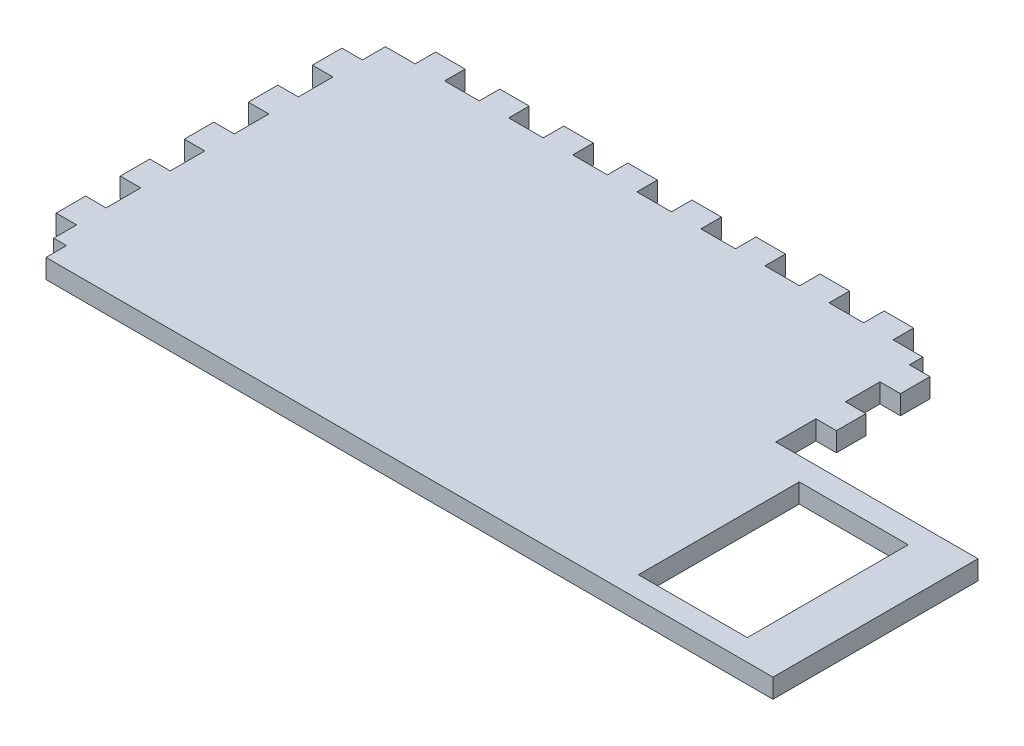
SolidWorks part; units mm, degrees
ref_plane "Front Plane" through (0, 0, 0) normal (0, 0, 1) x (1, 0, 0)
ref_plane "Top Plane" through (0, 0, 0) normal (0, 1, 0) x (1, 0, 0)
ref_plane "Right Plane" through (0, 0, 0) normal (1, 0, 0) x (0, 0, -1)
sketch "Sketch1" plane through (0, 0, 0) normal (0, 1, 0) x (1, 0, 0)
  line L63 (-28.8972, -2.2822) -> (-28.8972, -7.6797)
  line L64 (-28.8972, 35.9003) -> (-24.2472, 35.9003)
  line L65 (-28.8972, 35.9003) -> (-28.8972, 32.3103)
  line L66 (-28.8972, 7.7153) -> (-28.8972, 2.3178)
  line L67 (-28.8972, -15.8697) -> (-26.8972, -15.8697)
  line L68 (-28.8972, 17.7128) -> (-28.8972, 12.3153)
  line L69 (55.0028, 35.9003) -> (55.0028, 33.8003)
  line L70 (-28.8972, 27.7103) -> (-28.8972, 22.3128)
  line L71 (-28.8972, -7.6797) -> (-32.0972, -7.6797)
  line L73 (-28.8972, -12.2797) -> (-32.0972, -12.2797)
  line L74 (-32.0972, -7.6797) -> (-32.0972, -12.2797)
  line L75 (-28.8972, 2.3178) -> (-32.0972, 2.3178)
  line L76 (-32.0972, 2.3178) -> (-32.0972, -2.2822)
  line L77 (-28.8972, -2.2822) -> (-32.0972, -2.2822)
  line L79 (-28.8972, 12.3153) -> (-32.0972, 12.3153)
  line L80 (-32.0972, 12.3153) -> (-32.0972, 7.7153)
  line L89 (-28.8972, 7.7153) -> (-32.0972, 7.7153)
  line L90 (-28.8972, -15.8697) -> (-28.8972, -12.2797)
  line L91 (-14.2472, 35.9003) -> (-14.2472, 39.1003)
  line L93 (-28.8972, 22.3128) -> (-32.0972, 22.3128)
  line L94 (-32.0972, 22.3128) -> (-32.0972, 17.7128)
  line L95 (-28.8972, 17.7128) -> (-32.0972, 17.7128)
  line L97 (-28.8972, 32.3103) -> (-32.0972, 32.3103)
  line L98 (-32.0972, 32.3103) -> (-32.0972, 27.7103)
  line L99 (-28.8972, 27.7103) -> (-32.0972, 27.7103)
  line L101 (-24.2472, 35.9003) -> (-24.2472, 39.1003)
  line L102 (-24.2472, 39.1003) -> (-19.6472, 39.1003)
  line L103 (-19.6472, 35.9003) -> (-19.6472, 39.1003)
  line L105 (-9.6472, 35.9003) -> (-9.6472, 39.1003)
  line L106 (-14.2472, 39.1003) -> (-9.6472, 39.1003)
  line L107 (-4.2472, 35.9003) -> (-4.2472, 39.1003)
  line L109 (0.3528, 35.9003) -> (0.3528, 39.1003)
  line L110 (-4.2472, 39.1003) -> (0.3528, 39.1003)
  line L111 (5.7528, 35.9003) -> (5.7528, 39.1003)
  line L113 (10.3528, 35.9003) -> (10.3528, 39.1003)
  line L114 (5.7528, 39.1003) -> (10.3528, 39.1003)
  line L115 (15.7528, 35.9003) -> (15.7528, 39.1003)
  line L117 (20.3528, 35.9003) -> (20.3528, 39.1003)
  line L118 (15.7528, 39.1003) -> (20.3528, 39.1003)
  line L119 (25.7528, 35.9003) -> (25.7528, 39.1003)
  line L121 (30.3528, 35.9003) -> (30.3528, 39.1003)
  line L122 (25.7528, 39.1003) -> (30.3528, 39.1003)
  line L123 (35.7528, 35.9003) -> (35.7528, 39.1003)
  line L125 (40.3528, 35.9003) -> (40.3528, 39.1003)
  line L126 (35.7528, 39.1003) -> (40.3528, 39.1003)
  line L127 (45.7528, 35.9003) -> (45.7528, 39.1003)
  line L129 (50.3528, 35.9003) -> (50.3528, 39.1003)
  line L130 (45.7528, 39.1003) -> (50.3528, 39.1003)
  line L131 (-19.6472, 35.9003) -> (-14.2472, 35.9003)
  line L132 (-9.6472, 35.9003) -> (-4.2472, 35.9003)
  line L133 (0.3528, 35.9003) -> (5.7528, 35.9003)
  line L134 (10.3528, 35.9003) -> (15.7528, 35.9003)
  line L135 (20.3528, 35.9003) -> (25.7528, 35.9003)
  line L136 (30.3528, 35.9003) -> (35.7528, 35.9003)
  line L137 (40.3528, 35.9003) -> (45.7528, 35.9003)
  line L138 (50.3528, 35.9003) -> (55.0028, 35.9003)
  line L139 (55.0028, 29.2003) -> (55.0028, 23.8003)
  line L140 (55.0028, 33.8003) -> (58.2028, 33.8003)
  line L142 (55.0028, 29.2003) -> (58.2028, 29.2003)
  line L143 (58.2028, 33.8003) -> (58.2028, 29.2003)
  line L144 (55.0028, 19.2003) -> (58.2028, 19.2003)
  line L146 (55.0028, 23.8003) -> (58.2028, 23.8003)
  line L147 (58.2028, 19.2003) -> (58.2028, 23.8003)
  line L149 (55.0028, 19.2003) -> (55.0028, 12.9303)
  line L151 (-26.8972, -15.8697) -> (-26.8972, -19.0697)
  line L152 (-26.8972, -19.0697) -> (55.0028, -19.0697)
  line L155 (55.0028, -19.0697) -> (86.5728, -19.0697)
  line L157 (55.0028, 12.9303) -> (86.5728, 12.9303)
  line L158 (86.5728, -19.0697) -> (86.5728, 12.9303)
  dimension "D1" = 83.9
  dimension "D2" = 51.77
  dimension "D3" = 3.2
  dimension "D4" = 4.6
  dimension "D5" = 3.59
  dimension "D7" = 3.59
  dimension "D8" = 4.6
  dimension "D9" = 5.3975
  dimension "D11" = 4.65
  dimension "D10" = 3.2
  dimension "D12" = 4.6
  dimension "D14" = 4.65
  dimension "D15" = 3.2
  dimension "D16" = 4.6
  dimension "D17" = 4.6
  dimension "D18" = 5.4
  dimension "D19" = 2.1
  dimension "D20" = 2
  dimension "D21" = 3.2
  dimension "D22" = 32
  dimension "D23" = 31.57
  dimension "D6" = 5
  dimension "D13" = 8
extrude "Boss-Extrude3" add sketch "Sketch1" along normal blind 3
sketch "Sketch2" plane through (0, 3, 0) normal (0, 1, 0) x (1, 0, 0)
  line L0 (86.5728, -19.0697) -> (86.5728, 12.9303) construction
  line L1 (62.2328, 9.3703) -> (79.2328, 9.3703)
  line L2 (62.2328, 9.3703) -> (62.2328, -15.7297)
  line L3 (62.2328, -15.7297) -> (79.2328, -15.7297)
  line L4 (79.2328, 9.3703) -> (79.2328, -15.7297)
  line L5 (86.5728, 12.9303) -> (55.0028, 12.9303) construction
  dimension "D1" = 7.34
  dimension "D2" = 17
  dimension "D3" = 3.56
  dimension "D4" = 25.1
extrude "Cut-Extrude1" cut sketch "Sketch2" against normal blind 3
